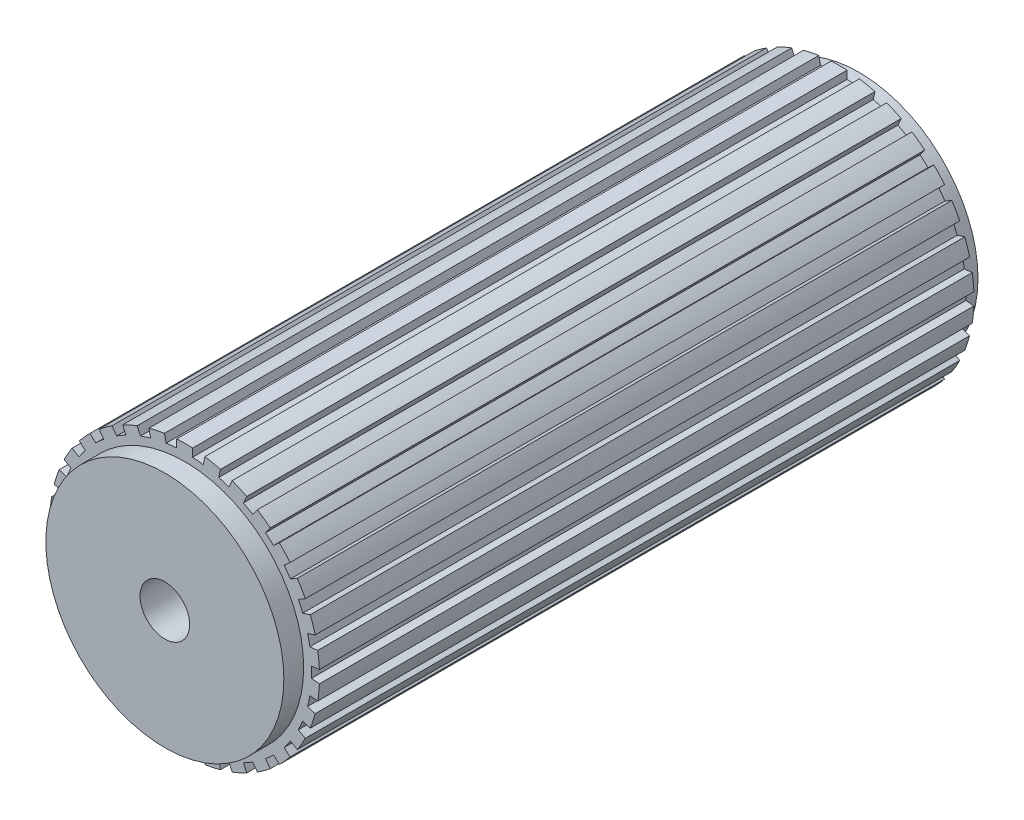
SolidWorks part; units mm, degrees
ref_plane "Front Plane" through (0, 0, 0) normal (0, 0, 1) x (1, 0, 0)
ref_plane "Top Plane" through (0, 0, 0) normal (0, 1, 0) x (1, 0, 0)
ref_plane "Right Plane" through (0, 0, 0) normal (1, 0, 0) x (0, 0, -1)
sketch "Sketch1" plane through (0, 0, 0) normal (0, 0, 1) x (1, 0, 0)
  circle A0 centre (0, 0) radius 60
  circle A1 centre (0, 0) radius 12.5
  dimension "D1" = 120
  dimension "D2" = 25
extrude "Boss-Extrude1" add sketch "Sketch1" along normal blind 350
ref_plane "Plane1" through (0, 0, 340) normal (0, 0, 1) x (1, 0, 0)
sketch "Sketch2" plane through (0, 0, 340) normal (0, 0, 1) x (1, 0, 0)
  line L0 (0, 0) -> (0, 76.7806) construction
  line L1 (9.3677, 63.3107) -> (10.2009, 67.2305)
  line L2 (17.1929, 61.6474) -> (18.0261, 65.5672)
  line L3 (22.3261, 59.9796) -> (23.956, 63.6405)
  line L4 (29.6344, 56.7257) -> (31.2644, 60.3866)
  line L5 (-4, 63.8749) -> (-4, 67.8823)
  line L6 (4, 63.8749) -> (4, 67.8823)
  line L7 (34.3086, 54.027) -> (36.6641, 57.269)
  line L8 (40.7808, 49.3247) -> (43.1363, 52.5668)
  line L9 (44.7918, 45.7132) -> (47.7698, 48.3947)
  line L10 (50.1448, 39.7681) -> (53.1229, 42.4495)
  line L11 (53.3173, 35.4015) -> (56.7878, 37.4052)
  line L12 (57.3173, 28.4733) -> (60.7878, 30.477)
  line L13 (59.5126, 23.5426) -> (63.3238, 24.781)
  line L14 (61.9847, 15.9342) -> (65.7959, 17.1725)
  line L15 (63.1069, 10.6548) -> (67.0923, 11.0737)
  line L16 (63.9431, 2.6987) -> (67.9285, 3.1175)
  line L17 (63.9431, -2.6987) -> (67.9285, -3.1175)
  line L18 (63.1069, -10.6548) -> (67.0923, -11.0737)
  line L19 (61.9847, -15.9342) -> (65.7959, -17.1725)
  line L20 (59.5126, -23.5426) -> (63.3238, -24.781)
  line L21 (57.3173, -28.4733) -> (60.7878, -30.477)
  line L22 (53.3173, -35.4015) -> (56.7878, -37.4052)
  line L23 (50.1448, -39.7681) -> (53.1229, -42.4495)
  line L24 (44.7918, -45.7132) -> (47.7698, -48.3947)
  line L25 (40.7808, -49.3247) -> (43.1363, -52.5668)
  line L26 (34.3086, -54.027) -> (36.6641, -57.269)
  line L27 (29.6344, -56.7257) -> (31.2644, -60.3866)
  line L28 (22.3261, -59.9796) -> (23.956, -63.6405)
  line L29 (17.1929, -61.6474) -> (18.0261, -65.5672)
  line L30 (9.3677, -63.3107) -> (10.2009, -67.2305)
  line L31 (4, -63.8749) -> (4, -67.8823)
  line L32 (-4, -63.8749) -> (-4, -67.8823)
  line L33 (-9.3677, -63.3107) -> (-10.2009, -67.2305)
  line L34 (-17.1929, -61.6474) -> (-18.0261, -65.5672)
  line L35 (-22.3261, -59.9796) -> (-23.956, -63.6405)
  line L36 (-29.6344, -56.7257) -> (-31.2644, -60.3866)
  line L37 (-34.3086, -54.027) -> (-36.6641, -57.269)
  line L38 (-40.7808, -49.3247) -> (-43.1363, -52.5668)
  line L39 (-44.7918, -45.7132) -> (-47.7698, -48.3947)
  line L40 (-50.1448, -39.7681) -> (-53.1229, -42.4495)
  line L41 (-53.3173, -35.4015) -> (-56.7878, -37.4052)
  line L42 (-57.3173, -28.4733) -> (-60.7878, -30.477)
  line L43 (-59.5126, -23.5426) -> (-63.3238, -24.781)
  line L44 (-61.9847, -15.9342) -> (-65.7959, -17.1725)
  line L45 (-63.1069, -10.6548) -> (-67.0923, -11.0737)
  line L46 (-63.9431, -2.6987) -> (-67.9285, -3.1175)
  line L47 (-63.9431, 2.6987) -> (-67.9285, 3.1175)
  line L48 (-63.1069, 10.6548) -> (-67.0923, 11.0737)
  line L49 (-61.9847, 15.9342) -> (-65.7959, 17.1725)
  line L50 (-59.5126, 23.5426) -> (-63.3238, 24.781)
  line L51 (-57.3173, 28.4733) -> (-60.7878, 30.477)
  line L52 (-53.3173, 35.4015) -> (-56.7878, 37.4052)
  line L53 (-50.1448, 39.7681) -> (-53.1229, 42.4495)
  line L54 (-44.7918, 45.7132) -> (-47.7698, 48.3947)
  line L55 (-40.7808, 49.3247) -> (-43.1363, 52.5668)
  line L56 (-34.3086, 54.027) -> (-36.6641, 57.269)
  line L57 (-29.6344, 56.7257) -> (-31.2644, 60.3866)
  line L58 (-22.3261, 59.9796) -> (-23.956, 63.6405)
  line L59 (-17.1929, 61.6474) -> (-18.0261, 65.5672)
  line L60 (-9.3677, 63.3107) -> (-10.2009, 67.2305)
  circle A0 centre (0, 0) radius 60 construction
  circle A1 centre (0, 0) radius 60
  arc A2 (4, 67.8823) -> (-4, 67.8823) centre (0, 0) ccw
  arc A3 (-4, 63.8749) -> (-9.3677, 63.3107) centre (0, 0) ccw
  circle A4 centre (0, 0) radius 68 construction
  circle A5 centre (0, 0) radius 64 construction
  arc A6 (18.0261, 65.5672) -> (10.2009, 67.2305) centre (0, 0) ccw
  arc A7 (31.2644, 60.3866) -> (23.956, 63.6405) centre (0, 0) ccw
  arc A8 (43.1363, 52.5668) -> (36.6641, 57.269) centre (0, 0) ccw
  arc A9 (53.1229, 42.4495) -> (47.7698, 48.3947) centre (0, 0) ccw
  arc A10 (60.7878, 30.477) -> (56.7878, 37.4052) centre (0, 0) ccw
  arc A11 (65.7959, 17.1725) -> (63.3238, 24.781) centre (0, 0) ccw
  arc A12 (67.9285, 3.1175) -> (67.0923, 11.0737) centre (0, 0) ccw
  arc A13 (67.0923, -11.0737) -> (67.9285, -3.1175) centre (0, 0) ccw
  arc A14 (63.3238, -24.781) -> (65.7959, -17.1725) centre (0, 0) ccw
  arc A15 (56.7878, -37.4052) -> (60.7878, -30.477) centre (0, 0) ccw
  arc A16 (47.7698, -48.3947) -> (53.1229, -42.4495) centre (0, 0) ccw
  arc A17 (36.6641, -57.269) -> (43.1363, -52.5668) centre (0, 0) ccw
  arc A18 (23.956, -63.6405) -> (31.2644, -60.3866) centre (0, 0) ccw
  arc A19 (10.2009, -67.2305) -> (18.0261, -65.5672) centre (0, 0) ccw
  arc A20 (-4, -67.8823) -> (4, -67.8823) centre (0, 0) ccw
  arc A21 (-18.0261, -65.5672) -> (-10.2009, -67.2305) centre (0, 0) ccw
  arc A22 (-31.2644, -60.3866) -> (-23.956, -63.6405) centre (0, 0) ccw
  arc A23 (-43.1363, -52.5668) -> (-36.6641, -57.269) centre (0, 0) ccw
  arc A24 (-53.1229, -42.4495) -> (-47.7698, -48.3947) centre (0, 0) ccw
  arc A25 (-60.7878, -30.477) -> (-56.7878, -37.4052) centre (0, 0) ccw
  arc A26 (-65.7959, -17.1725) -> (-63.3238, -24.781) centre (0, 0) ccw
  arc A27 (-67.9285, -3.1175) -> (-67.0923, -11.0737) centre (0, 0) ccw
  arc A28 (-67.0923, 11.0737) -> (-67.9285, 3.1175) centre (0, 0) ccw
  arc A29 (-63.3238, 24.781) -> (-65.7959, 17.1725) centre (0, 0) ccw
  arc A30 (-56.7878, 37.4052) -> (-60.7878, 30.477) centre (0, 0) ccw
  arc A31 (-47.7698, 48.3947) -> (-53.1229, 42.4495) centre (0, 0) ccw
  arc A32 (-36.6641, 57.269) -> (-43.1363, 52.5668) centre (0, 0) ccw
  arc A33 (-23.956, 63.6405) -> (-31.2644, 60.3866) centre (0, 0) ccw
  arc A34 (-10.2009, 67.2305) -> (-18.0261, 65.5672) centre (0, 0) ccw
  arc A35 (-17.1929, 61.6474) -> (-22.3261, 59.9796) centre (0, 0) ccw
  arc A36 (-29.6344, 56.7257) -> (-34.3086, 54.027) centre (0, 0) ccw
  arc A37 (-40.7808, 49.3247) -> (-44.7918, 45.7132) centre (0, 0) ccw
  arc A38 (-50.1448, 39.7681) -> (-53.3173, 35.4015) centre (0, 0) ccw
  arc A39 (-57.3173, 28.4733) -> (-59.5126, 23.5426) centre (0, 0) ccw
  arc A40 (-61.9847, 15.9342) -> (-63.1069, 10.6548) centre (0, 0) ccw
  arc A41 (-63.9431, 2.6987) -> (-63.9431, -2.6987) centre (0, 0) ccw
  arc A42 (-63.1069, -10.6548) -> (-61.9847, -15.9342) centre (0, 0) ccw
  arc A43 (-59.5126, -23.5426) -> (-57.3173, -28.4733) centre (0, 0) ccw
  arc A44 (-53.3173, -35.4015) -> (-50.1448, -39.7681) centre (0, 0) ccw
  arc A45 (-44.7918, -45.7132) -> (-40.7808, -49.3247) centre (0, 0) ccw
  arc A46 (-34.3086, -54.027) -> (-29.6344, -56.7257) centre (0, 0) ccw
  arc A47 (-22.3261, -59.9796) -> (-17.1929, -61.6474) centre (0, 0) ccw
  arc A48 (-9.3677, -63.3107) -> (-4, -63.8749) centre (0, 0) ccw
  arc A49 (4, -63.8749) -> (9.3677, -63.3107) centre (0, 0) ccw
  arc A50 (17.1929, -61.6474) -> (22.3261, -59.9796) centre (0, 0) ccw
  arc A51 (29.6344, -56.7257) -> (34.3086, -54.027) centre (0, 0) ccw
  arc A52 (40.7808, -49.3247) -> (44.7918, -45.7132) centre (0, 0) ccw
  arc A53 (50.1448, -39.7681) -> (53.3173, -35.4015) centre (0, 0) ccw
  arc A54 (57.3173, -28.4733) -> (59.5126, -23.5426) centre (0, 0) ccw
  arc A55 (61.9847, -15.9342) -> (63.1069, -10.6548) centre (0, 0) ccw
  arc A56 (63.9431, -2.6987) -> (63.9431, 2.6987) centre (0, 0) ccw
  arc A57 (63.1069, 10.6548) -> (61.9847, 15.9342) centre (0, 0) ccw
  arc A58 (59.5126, 23.5426) -> (57.3173, 28.4733) centre (0, 0) ccw
  arc A59 (53.3173, 35.4015) -> (50.1448, 39.7681) centre (0, 0) ccw
  arc A60 (44.7918, 45.7132) -> (40.7808, 49.3247) centre (0, 0) ccw
  arc A61 (34.3086, 54.027) -> (29.6344, 56.7257) centre (0, 0) ccw
  arc A62 (22.3261, 59.9796) -> (17.1929, 61.6474) centre (0, 0) ccw
  arc A63 (9.3677, 63.3107) -> (4, 63.8749) centre (0, 0) ccw
  point P131 (0, 0)
  dimension "D1" = 8
  dimension "D2" = 4
  dimension "D3" = 30
extrude "Boss-Extrude2" add sketch "Sketch2" against normal blind 330
ref_plane "Plane2" through (0, 0, 175) normal (0, 0, -1) x (-1, 0, 0)
